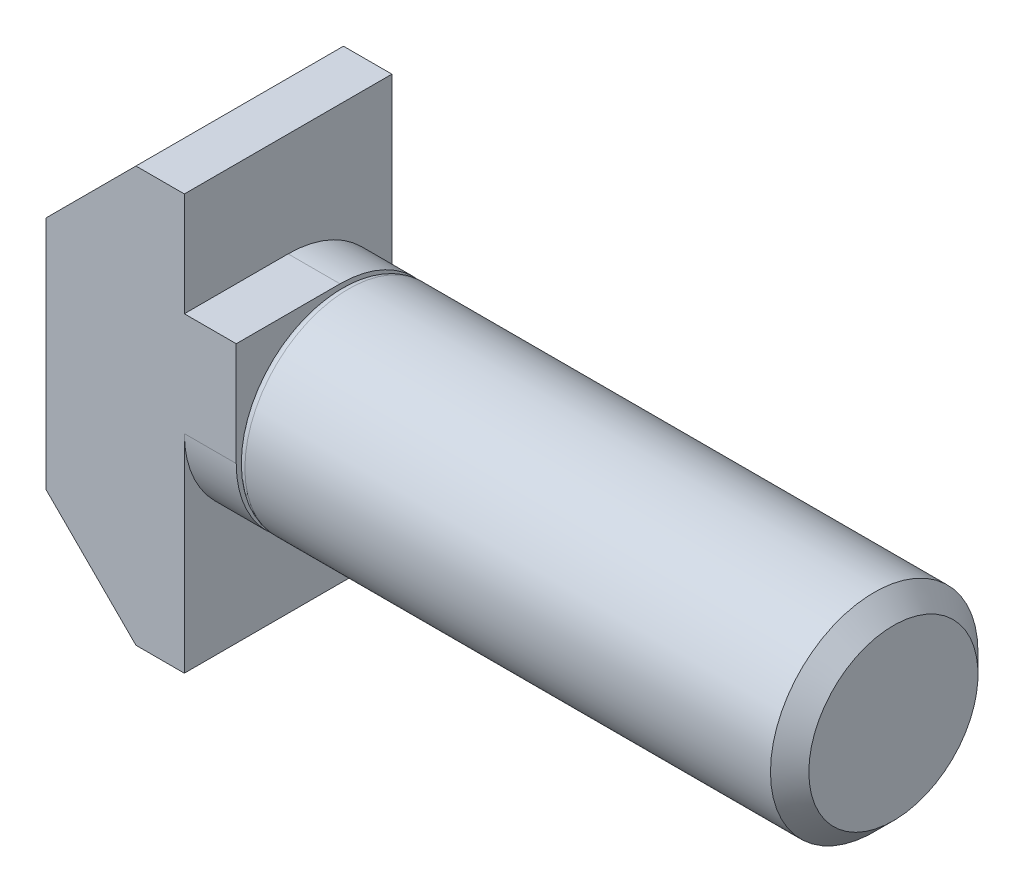
SolidWorks part; units mm, degrees
ref_plane "Plane1" through (0, 0, 0) normal (0, 0, 1) x (1, 0, 0)
ref_plane "Plane2" through (0, 0, 0) normal (0, 1, 0) x (1, 0, 0)
ref_plane "Plane3" through (0, 0, 0) normal (1, 0, 0) x (0, 0, -1)
sketch "BodySke" plane through (0, 0, 0) normal (0, 0, 1) x (1, 0, 0)
  line L2 (0, 0) -> (0, 3)
  line L3 (0, 3) -> (15.4455, 3)
  line L4 (16, 2.4455) -> (16, 0)
  line L5 (16, 0) -> (0, 0)
  line L6 (-31.75, 0) -> (127, 0) construction
  line L8 (16, 2.4455) -> (15.4455, 3)
  line L10 (16, -2.4455) -> (15.4455, -3) construction
  dimension "Diameter" = 6
  dimension "Length" = 16
  dimension "Body_ch_ang" = 45
  dimension "Minor_dia" = 4.891
revolve "Base-Revolve" add sketch "BodySke" angle 360 about L6
fillet "Fillet1" radius 0.25 1 edges at (0, 0, 3)
sketch "Sketch1" plane through (0, 0, 0) normal (0, 0, 1) x (1, 0, 0)
  line L0 (59.6971, 544.074) -> (369.0304, 544.074) construction
  line L1 (-5.5, -3.4) -> (-5.5, 3.4)
  line L2 (-5.5, 3.4) -> (-2.9, 6)
  line L3 (-2.9, 6) -> (-1.5, 6)
  line L4 (-1.5, 6) -> (-1.5, 3)
  line L5 (-1.5, 3) -> (0, 3)
  line L6 (0, 3) -> (0, -3)
  line L8 (0, 0) -> (-2.0861, 0) construction
  line L9 (-1.5, -3) -> (0, -3)
  line L10 (-1.5, -6) -> (-1.5, -3)
  line L11 (-2.9, -6) -> (-1.5, -6)
  line L12 (-5.5, -3.4) -> (-2.9, -6)
  line L13 (0, 2.75) -> (0, -2.75) construction
  point P12 (0, 0)
  dimension "D1" = 12
  dimension "D2" = 5.5
  dimension "D3" = 6
  dimension "D4" = 1.5
  dimension "D5" = 6.8
  dimension "D6" = 1.4
extrude "Boss-Extrude1" add sketch "Sketch1" along normal mid plane 6
fillet "Fillet2" radius 3 2 edges at (-0.75, -3, 3) (-0.75, 3, -3)
